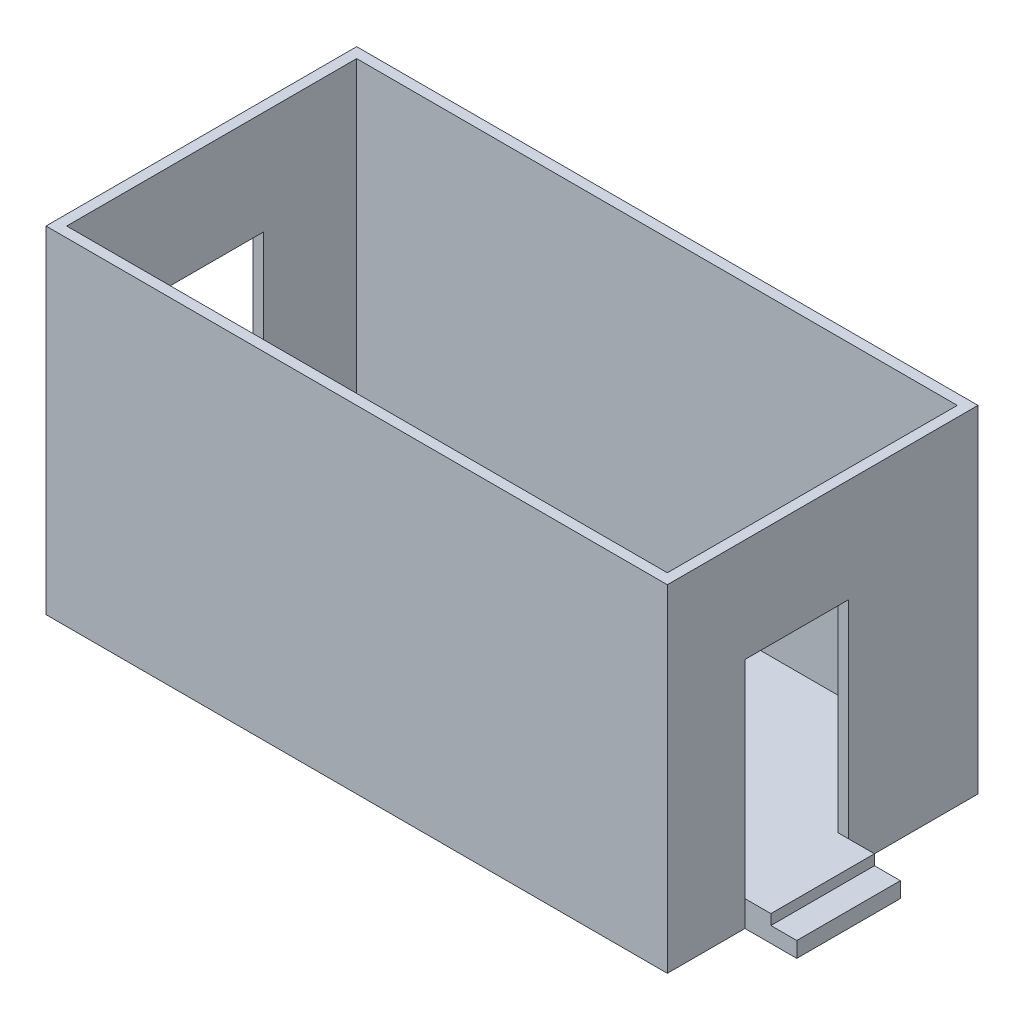
SolidWorks part; units mm, degrees
ref_plane "Front Plane" through (0, 0, 0) normal (0, 0, 1) x (1, 0, 0)
ref_plane "Top Plane" through (0, 0, 0) normal (0, 1, 0) x (1, 0, 0)
ref_plane "Right Plane" through (0, 0, 0) normal (1, 0, 0) x (0, 0, -1)
sketch "Sketch1" plane through (0, 0, 0) normal (0, 1, 0) x (1, 0, 0)
  line L1 (-3000, 1500) -> (3000, 1500)
  line L2 (-3000, 1500) -> (-3000, -1500)
  line L3 (-3000, -1500) -> (3000, -1500)
  line L4 (3000, 1500) -> (3000, -1500)
  line L5 (-3000, 1500) -> (3000, -1500) construction
  line L6 (-3000, -1500) -> (3000, 1500) construction
  point P0 (0, 0)
  dimension "D1" = 6000
  dimension "D2" = 3000
extrude "Boss-Extrude1" add sketch "Sketch1" along normal blind 250
sketch "Sketch2" plane through (0, 250, 0) normal (0, 1, 0) x (1, 0, 0)
  line L0 (-2900, 1400) -> (2900, 1400)
  line L1 (-3000, 1500) -> (3000, 1500)
  line L2 (-3000, 1500) -> (-3000, -1500)
  line L3 (-3000, -1500) -> (3000, -1500)
  line L4 (3000, 1500) -> (3000, -1500)
  line L5 (2900, 1400) -> (2900, -1400)
  line L6 (-2900, -1400) -> (2900, -1400)
  line L7 (-2900, 1400) -> (-2900, -1400)
  dimension "D1" = 100
extrude "Boss-Extrude2" add sketch "Sketch2" along normal blind 3000
sketch "Sketch3" plane through (-3000, 0, 0) normal (-1, 0, 0) x (0, 0, 1)
  line L0 (-1500, 0) -> (1500, 0) construction
  line L1 (-500, 2250) -> (500, 2250)
  line L2 (-500, 2250) -> (-500, 250)
  line L3 (-500, 250) -> (500, 250)
  line L4 (500, 2250) -> (500, 250)
  line L5 (1500, 3250) -> (1500, 0) construction
  dimension "D1" = 2000
  dimension "D2" = 250
  dimension "D3" = 1000
  dimension "D4" = 1000
extrude "Cut-Extrude1" cut sketch "Sketch3" against normal blind 250
sketch "Sketch4" plane through (3000, 0, 0) normal (1, 0, 0) x (0, 0, -1)
  line L0 (-1500, 0) -> (1500, 0) construction
  line L1 (-750, 2250) -> (250, 2250)
  line L2 (-750, 2250) -> (-750, 250)
  line L3 (-750, 250) -> (250, 250)
  line L4 (250, 2250) -> (250, 250)
  line L5 (-1500, 3250) -> (-1500, 0) construction
  dimension "D1" = 250
  dimension "D2" = 1000
  dimension "D3" = 2000
  dimension "D4" = 750
extrude "Cut-Extrude2" cut sketch "Sketch4" against normal blind 250
sketch "Sketch6" plane through (3000, 0, 0) normal (1, 0, 0) x (0, 0, -1)
  line L0 (-1500, 0) -> (1500, 0) construction
  line L1 (-750, 250) -> (250, 250)
  line L2 (-750, 250) -> (-750, 0)
  line L3 (-750, 0) -> (250, 0)
  line L4 (250, 250) -> (250, 0)
  dimension "D1" = 1000
extrude "Boss-Extrude4" add sketch "Sketch6" along normal blind 500
sketch "Sketch7" plane through (-3000, 0, 0) normal (-1, 0, 0) x (0, 0, 1)
  line L0 (-1500, 0) -> (1500, 0) construction
  line L1 (-500, 250) -> (500, 250)
  line L2 (-500, 250) -> (-500, 0)
  line L3 (-500, 0) -> (500, 0)
  line L4 (500, 250) -> (500, 0)
  dimension "D1" = 1000
extrude "Boss-Extrude5" add sketch "Sketch7" along normal blind 500
sketch "Sketch8" plane through (0, 250, 0) normal (0, 1, 0) x (1, 0, 0)
  line L0 (3500, -750) -> (3000, -750) construction
  line L1 (3500, 250) -> (3250, 250)
  line L2 (3500, 250) -> (3500, -750)
  line L3 (3500, -750) -> (3250, -750)
  line L4 (3250, 250) -> (3250, -750)
  dimension "D1" = 250
extrude "Cut-Extrude4" cut sketch "Sketch8" against normal blind 100
sketch "Sketch9" plane through (0, 250, 0) normal (0, 1, 0) x (1, 0, 0)
  line L0 (-3500, -500) -> (-3000, -500) construction
  line L1 (-3500, 500) -> (-3250, 500)
  line L2 (-3500, 500) -> (-3500, -500)
  line L3 (-3500, -500) -> (-3250, -500)
  line L4 (-3250, 500) -> (-3250, -500)
  dimension "D1" = 250
extrude "Cut-Extrude5" cut sketch "Sketch9" against normal blind 100
